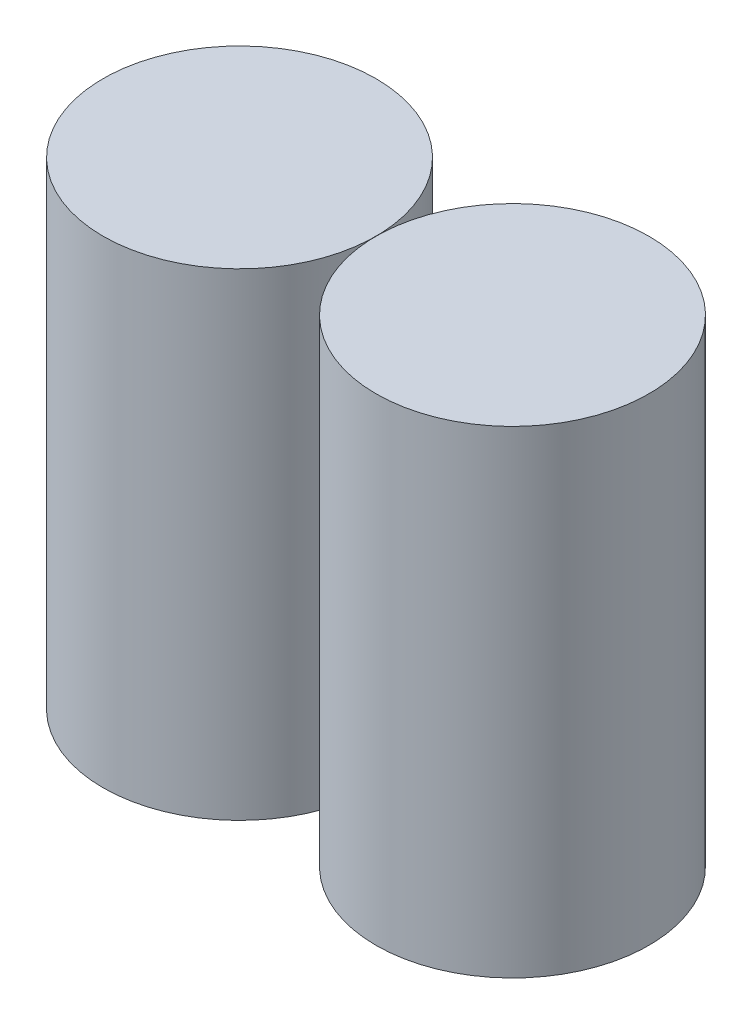
SolidWorks part; units mm, degrees
ref_plane "Front Plane" through (0, 0, 0) normal (0, 0, 1) x (1, 0, 0)
ref_plane "Top Plane" through (0, 0, 0) normal (0, 1, 0) x (1, 0, 0)
ref_plane "Right Plane" through (0, 0, 0) normal (1, 0, 0) x (0, 0, -1)
sketch "Sketch1" plane through (0, 0, 0) normal (0, 1, 0) x (1, 0, 0)
  circle A0 centre (0, 0) radius 12
  circle A1 centre (-24, 0) radius 12
  dimension "D1" = 24
  dimension "D2" = 24
extrude "Boss-Extrude1" add sketch "Sketch1" along normal blind 42 contours A0 | A1
